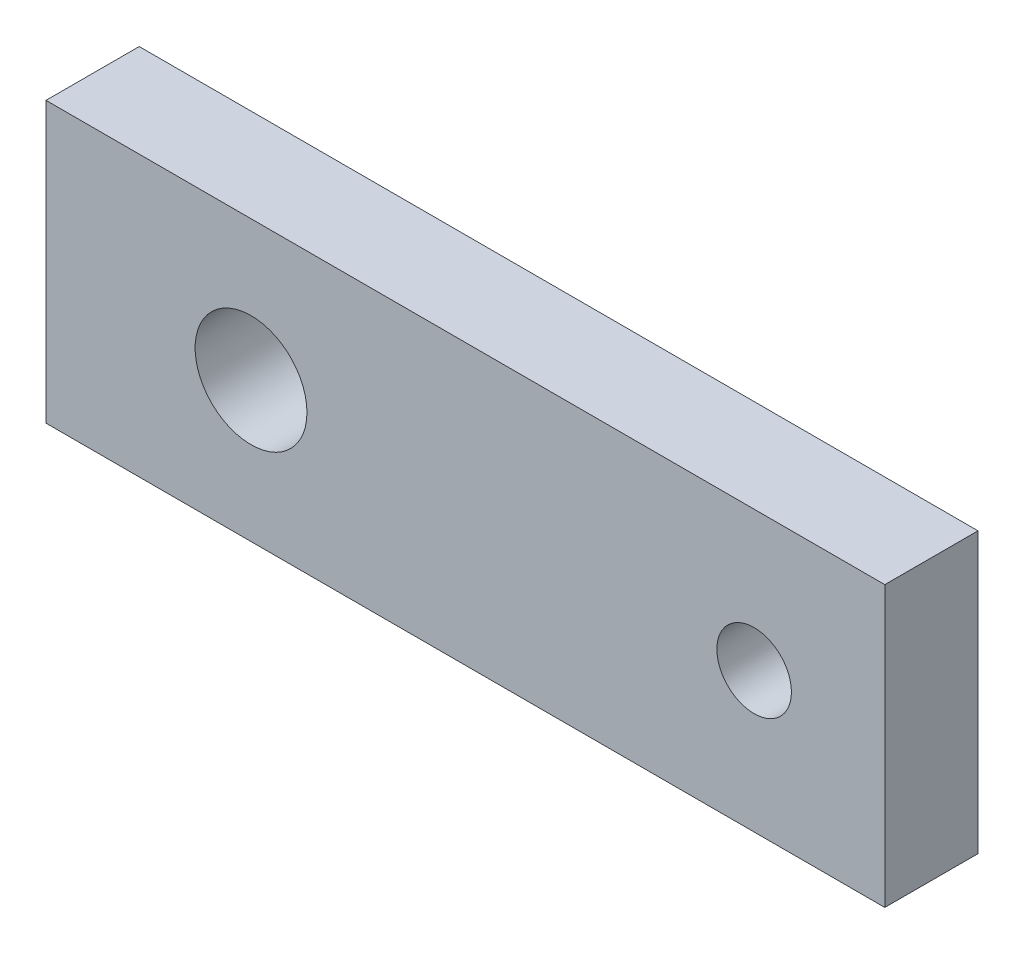
SolidWorks part; units mm, degrees
ref_plane "Ön Düzlem" through (0, 0, 0) normal (0, 0, 1) x (1, 0, 0)
ref_plane "Üst Düzlem" through (0, 0, 0) normal (0, 1, 0) x (1, 0, 0)
ref_plane "Sağ Düzlem" through (0, 0, 0) normal (1, 0, 0) x (0, 0, -1)
sketch "Sketch1" plane through (0, 0, 0) normal (0, 0, 1) x (1, 0, 0)
  line L0 (-23, 0) -> (30.98, 0) construction
  line L1 (-45, -15) -> (45, -15)
  line L2 (-45, -15) -> (-45, 15)
  line L3 (-45, 15) -> (45, 15)
  line L4 (45, -15) -> (45, 15)
  line L5 (-45, -15) -> (45, 15) construction
  line L6 (-45, 15) -> (45, -15) construction
  circle A0 centre (-23, 0) radius 6
  circle A1 centre (30.98, 0) radius 4
  point P0 (0, 0)
  dimension "D3" = 12
  dimension "D4" = 8
  dimension "D1" = 30
  dimension "D2" = 53.98
  dimension "D5" = 22
  dimension "D6" = 15
  dimension "D7" = 90
extrude "Boss-Extrude1" add sketch "Sketch1" along normal blind 10
